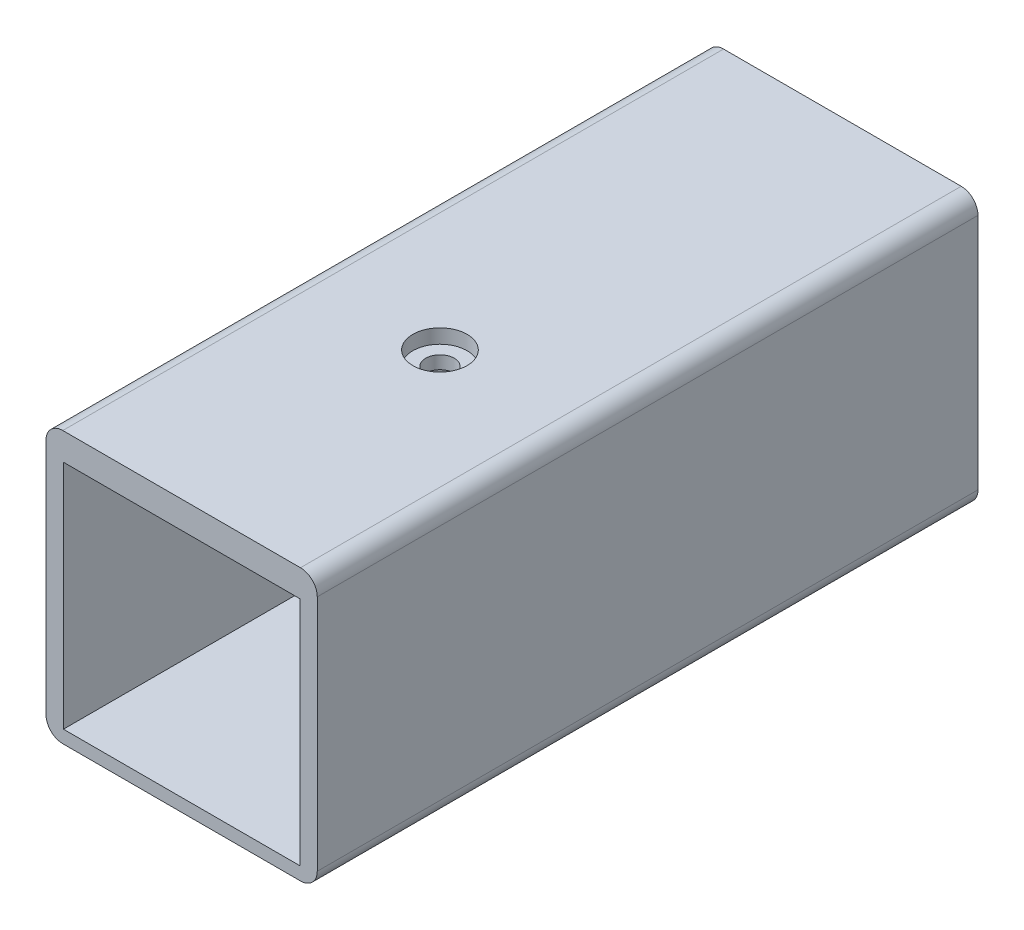
SolidWorks part; units mm, degrees
ref_plane "前视基准面" through (0, 0, 0) normal (0, 0, 1) x (1, 0, 0)
ref_plane "上视基准面" through (0, 0, 0) normal (0, 1, 0) x (1, 0, 0)
ref_plane "右视基准面" through (0, 0, 0) normal (1, 0, 0) x (0, 0, -1)
sketch "草图1" plane through (0, 0, 0) normal (0, 0, 1) x (1, 0, 0)
  line L1 (-9.2, -10.5) -> (9.2, -10.5)
  line L2 (-10.5, -9.2) -> (-10.5, 9.2)
  line L3 (-9.2, 10.5) -> (9.2, 10.5)
  line L4 (10.5, -9.2) -> (10.5, 9.2)
  line L5 (-10.5, -10.5) -> (10.5, 10.5) construction
  line L6 (-10.5, 10.5) -> (10.5, -10.5) construction
  arc A0 (-9.2, -10.5) -> (-10.5, -9.2) centre (-9.2, -9.2) cw
  arc A1 (9.2, -10.5) -> (10.5, -9.2) centre (9.2, -9.2) ccw
  arc A2 (9.2, 10.5) -> (10.5, 9.2) centre (9.2, 9.2) cw
  arc A3 (-10.5, 9.2) -> (-9.2, 10.5) centre (-9.2, 9.2) cw
  point P0 (0, 0)
  dimension "D3" = 1.3
  dimension "D1" = 21
  dimension "D2" = 21
extrude "凸台-拉伸1" add sketch "草图1" along normal blind 51.15
sketch "草图3" plane through (0, 0, 51.15) normal (0, 0, 1) x (1, 0, 0)
  line L0 (-9.2, -10.5) -> (9.2, -10.5) construction
  line L1 (-9.15, 8.4) -> (9.15, 8.4)
  line L2 (-9.15, 8.4) -> (-9.15, -9.5)
  line L3 (-9.15, -9.5) -> (9.15, -9.5)
  line L4 (9.15, 8.4) -> (9.15, -9.5)
  point P4 (0, -9.5)
  dimension "D1" = 18.3
  dimension "D2" = 17.9
  dimension "D3" = 1
extrude "切除-拉伸1" cut sketch "草图3" against normal offset from surface (50.35 mm away) 0.8 up to face at (0, 0, 0)
sketch "草图6" plane through (0, 0, 0.8) normal (0, 0, 1) x (1, 0, 0)
  line L0 (9.15, -9.5) -> (9.15, 8.4) construction
  line L1 (-9.15, -9.5) -> (9.15, -9.5)
  line L2 (-9.15, -9.5) -> (-9.15, -7)
  line L3 (-9.15, -7) -> (9.15, -7)
  line L4 (9.15, -9.5) -> (9.15, -7)
  dimension "D1" = 2.5
sketch "草图4" plane through (0, 0, 0) normal (0, 0, -1) x (-1, 0, 0)
  line L1 (-7.6, 7.1) -> (7.6, 7.1)
  line L2 (-7.6, 7.1) -> (-7.6, -5.3)
  line L3 (-7.6, -5.3) -> (7.6, -5.3)
  line L4 (7.6, 7.1) -> (7.6, -5.3)
  line L5 (9.15, -7) -> (-9.15, -7) construction
  point P4 (0, -5.3)
  dimension "D1" = 15.2
  dimension "D2" = 12.4
  dimension "D3" = 1.7
extrude "凸台-拉伸5" add sketch "草图6" along normal blind 2.5
extrude "切除-拉伸4" cut sketch "草图4" against normal blind 5.5
sketch "草图12" plane through (0, 10.5, 0) normal (0, 1, 0) x (1, 0, 0)
  line L0 (9.2, -51.15) -> (-9.2, -51.15) construction
  circle A0 centre (0, -31.15) radius 1.1
  point P5 (0, 0)
  dimension "D1" = 2.2
  dimension "D2" = 20
extrude "切除-拉伸5" cut sketch "草图12" against normal blind 7.5
sketch "草图13" plane through (0, 10.5, 0) normal (0, 1, 0) x (1, 0, 0)
  circle A0 centre (0, -31.15) radius 2.1
  dimension "D1" = 4.2
extrude "切除-拉伸6" cut sketch "草图13" against normal offset from surface (1.1 mm away) 1 up to face at (0, 8.4, 32.25)
sketch "草图14" plane through (-10.5, 0, 0) normal (-1, 0, 0) x (0, 0, 1)
  text T0 "USB - ETH" font "黑体" height 3
extrude "切除-拉伸7" cut sketch "草图14" against normal blind 0.4
